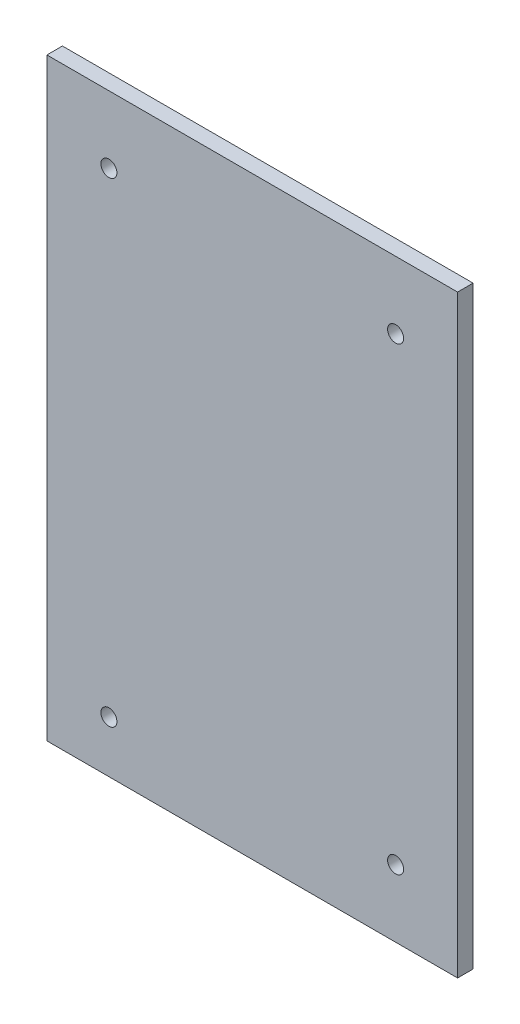
SolidWorks part; units mm, degrees
ref_plane "Front" through (0, 0, 0) normal (0, 0, 1) x (1, 0, 0)
ref_plane "Top" through (0, 0, 0) normal (0, 1, 0) x (1, 0, 0)
ref_plane "Right" through (0, 0, 0) normal (1, 0, 0) x (0, 0, -1)
sketch "Sketch1" plane through (0, 0, 0) normal (0, 0, 1) x (1, 0, 0)
  line L0 (0, 0) -> (-10.5808, 0) construction
  line L1 (-39.75, -57.5) -> (39.75, -57.5)
  line L2 (-39.75, -57.5) -> (-39.75, 57.5)
  line L3 (-39.75, 57.5) -> (39.75, 57.5)
  line L4 (39.75, -57.5) -> (39.75, 57.5)
  line L5 (-39.75, -57.5) -> (39.75, 57.5) construction
  line L6 (-39.75, 57.5) -> (39.75, -57.5) construction
  circle A0 centre (-27.75, 44.5) radius 1.55
  circle A1 centre (27.75, 44.5) radius 1.55
  circle A2 centre (27.75, -44.5) radius 1.55
  circle A3 centre (-27.75, -47.5) radius 1.55
  point P0 (0, 0)
  dimension "D3" = 3.1
  dimension "D4" = 3.1
  dimension "D5" = 13
  dimension "D6" = 12
  dimension "D7" = 12
  dimension "D10" = 12
  dimension "D11" = 3.1
  dimension "D12" = 13
  dimension "D13" = 3.1
  dimension "D1" = 115
  dimension "D2" = 79.5
  dimension "D8" = 10
  dimension "D9" = 12
extrude "Boss-Extrude1" add sketch "Sketch1" along normal blind 3
